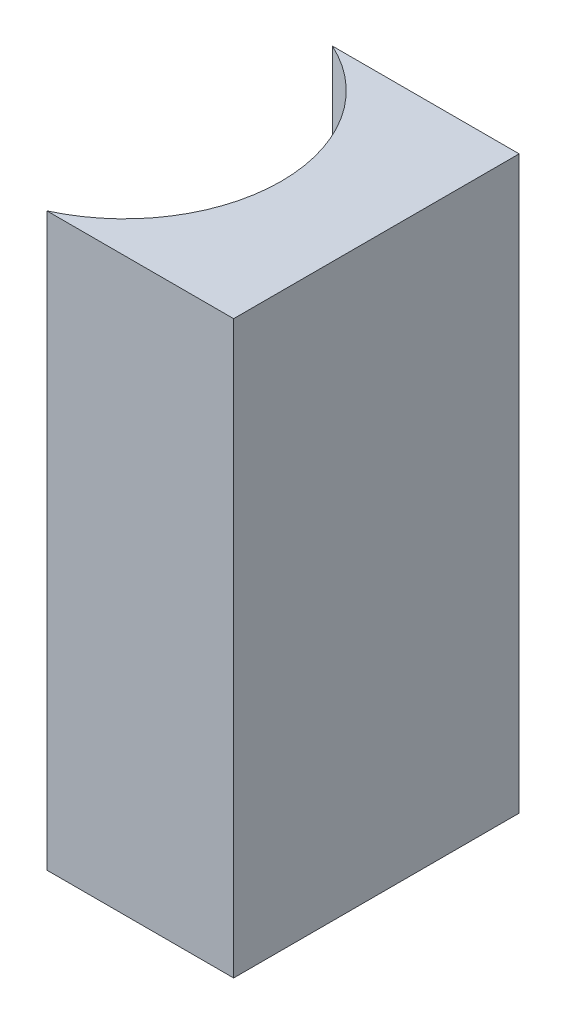
SolidWorks part; units mm, degrees
ref_plane "前视基准面" through (0, 0, 0) normal (0, 0, 1) x (1, 0, 0)
ref_plane "上视基准面" through (0, 0, 0) normal (0, 1, 0) x (1, 0, 0)
ref_plane "右视基准面" through (0, 0, 0) normal (1, 0, 0) x (0, 0, -1)
sketch "草图1" plane through (0, 0, 0) normal (0, 1, 0) x (1, 0, 0)
  line L0 (0, 0) -> (0, -6)
  line L1 (0, 0) -> (-3.9252, 0)
  line L2 (0, -6) -> (-3.9252, -6)
  line L3 (8.2336, -3) -> (-10.4405, -3) construction
  arc A0 (-3.9252, -6) -> (-3.9252, 0) centre (-5.3, -3) ccw
  point P7 (-2, -3)
  point P8 (0, -3)
  dimension "D2" = 3.3
  dimension "D3" = 2
  dimension "D1" = 6
extrude "凸台-拉伸1" add sketch "草图1" along normal blind 12
